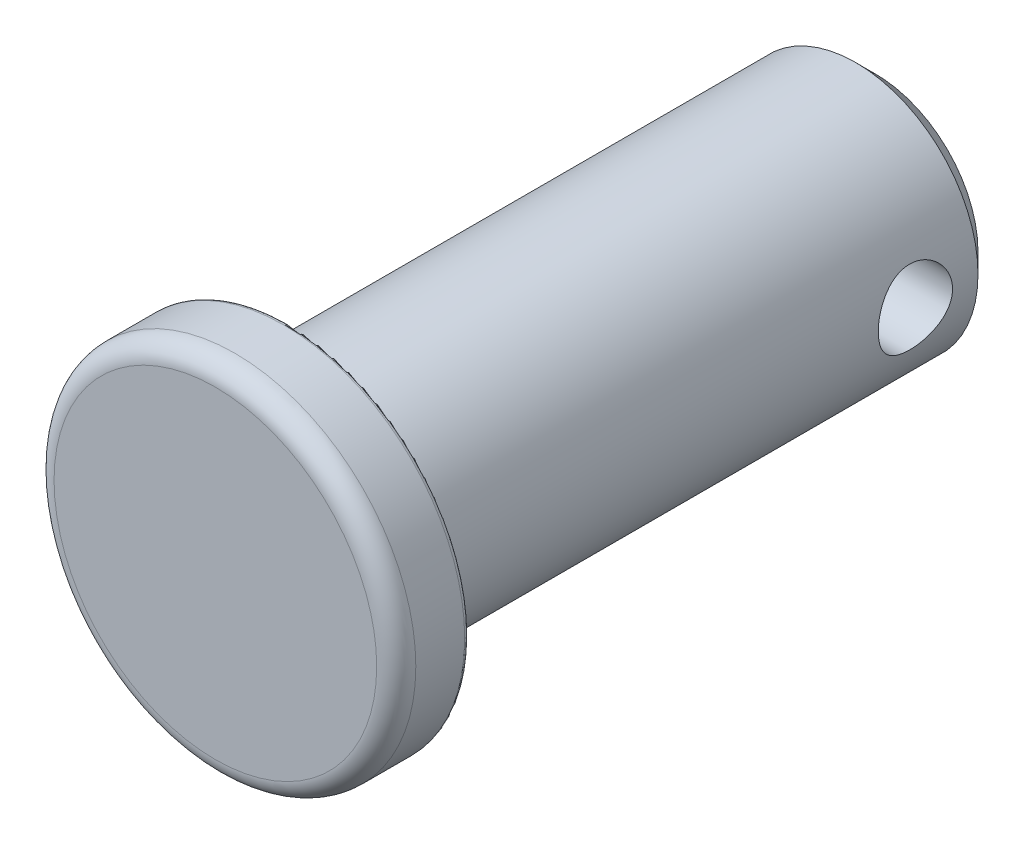
SolidWorks part; units mm, degrees
material "Alloy Steel"
ref_plane "Front Plane" through (0, 0, 0) normal (0, 0, 1) x (1, 0, 0)
ref_plane "Top Plane" through (0, 0, 0) normal (0, 1, 0) x (1, 0, 0)
ref_plane "Right Plane" through (0, 0, 0) normal (1, 0, 0) x (0, 0, -1)
sketch "Sketch1" plane through (0, 0, 0) normal (1, 0, 0) x (0, 0, -1)
  line L0 (0, 0) -> (84.6527, 0) construction
  line L1 (0, 0) -> (0, 4.191)
  line L2 (0.508, 4.699) -> (1.778, 4.699)
  line L3 (1.905, 4.572) -> (1.905, 3.175)
  line L4 (1.905, 3.175) -> (16.637, 3.175)
  line L5 (16.637, 3.175) -> (17.145, 2.667)
  line L6 (17.145, 2.667) -> (17.145, 0)
  line L7 (17.145, 0) -> (0, 0)
  arc A0 (0.508, 4.699) -> (0, 4.191) centre (0.508, 4.191) ccw
  arc A1 (1.905, 4.572) -> (1.778, 4.699) centre (1.778, 4.572) ccw
  point P11 (0, 4.699)
  dimension "D7" = 0.508
  dimension "D8" = 0.127
  dimension "D1" = 1.905
  dimension "D2" = 6.35
  dimension "D3" = 9.398
  dimension "D4" = 17.145
  dimension "D5" = 45
  dimension "D6" = 0.508
revolve "Revolve Base" add sketch "Sketch1" angle 360 about L0
sketch "Sketch2" plane through (0, 0, 0) normal (1, 0, 0) x (0, 0, -1)
  line L0 (0, 0) -> (15.0114, 0) construction
  line L2 (17.145, -2.667) -> (17.145, 2.667) construction
  circle A0 centre (15.0114, 0) radius 0.9652
  dimension "D1" = 1.9304
  dimension "D3" = 2.1336
extrude "Extrude1" cut sketch "Sketch2" against normal through all and the other way through all
